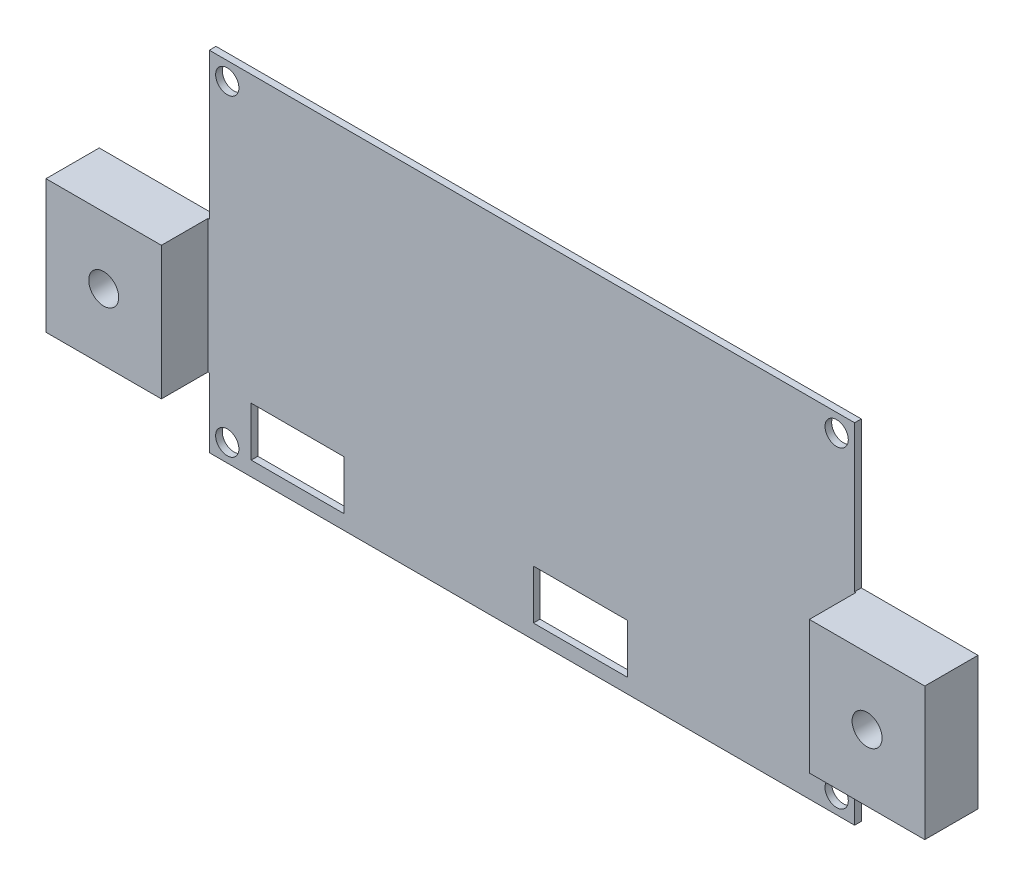
SolidWorks part; units mm, degrees
ref_plane "Front" through (0, 0, 0) normal (0, 0, 1) x (1, 0, 0)
ref_plane "Top" through (0, 0, 0) normal (0, 1, 0) x (1, 0, 0)
ref_plane "Right" through (0, 0, 0) normal (1, 0, 0) x (0, 0, -1)
sketch "Skizze1" plane through (0, 0, 0) normal (0, 0, 1) x (1, 0, 0)
  line L1 (0, 0) -> (97, 0)
  line L2 (0, 0) -> (0, 10.4)
  line L3 (0, 52.4) -> (97, 52.4)
  line L4 (97, 0) -> (97, 10.4)
  line L5 (6.2985, 2.1859) -> (20.2146, 2.1859)
  line L6 (6.2985, 2.1859) -> (6.2985, 9.5996)
  line L7 (6.2985, 9.5996) -> (20.2146, 9.5996)
  line L8 (20.2146, 2.1859) -> (20.2146, 9.5996)
  line L9 (48.5, 0) -> (48.5, -12.9781) construction
  line L11 (62.8756, 2.1859) -> (48.7166, 2.1859)
  line L12 (62.8756, 2.1859) -> (62.8756, 9.5996)
  line L13 (62.8756, 9.5996) -> (48.7166, 9.5996)
  line L14 (48.7166, 2.1859) -> (48.7166, 9.5996)
  line L15 (0, 30.4) -> (-17.5477, 30.4)
  line L16 (136.8695, 30.4) -> (-63.1305, 30.4) construction
  line L17 (-17.5477, 30.4) -> (-17.5477, 10.4)
  line L18 (136.8695, 10.4) -> (-63.1305, 10.4) construction
  line L19 (-17.5477, 10.4) -> (0, 10.4)
  line L20 (0, 30.4) -> (0, 52.4)
  line L21 (114.5477, 10.4) -> (97, 10.4)
  line L22 (114.5477, 30.4) -> (114.5477, 10.4)
  line L23 (97, 30.4) -> (114.5477, 30.4)
  line L24 (97, 30.4) -> (97, 52.4)
  circle A0 centre (94.3, 49.7) radius 1.75
  circle A1 centre (94.3, 2.7) radius 1.75
  circle A2 centre (2.7, 2.7) radius 1.75
  circle A3 centre (2.7, 49.7) radius 1.75
  point P40 (48.7166, 9.5996)
  dimension "D1" = 3.5
extrude "Aufsatz-Linear austragen1" add sketch "Skizze1" along normal blind 1
sketch "Skizze2" plane through (0, 0, 1) normal (0, 0, 1) x (1, 0, 0)
  line L0 (-17.5477, 30.4) -> (-17.5477, 10.4)
  line L1 (-17.5477, 10.4) -> (-0.2, 10.4)
  line L2 (-17.5477, 10.4) -> (0, 10.4) construction
  line L3 (-0.2, 10.4) -> (-0.2, 30.4)
  line L4 (0, 30.4) -> (-17.5477, 30.4) construction
  line L5 (-0.2, 30.4) -> (-17.5477, 30.4)
  line L6 (0, 52.4) -> (0, 0) construction
  line L7 (48.5, 0) -> (48.5, -21.6897)
  line L8 (0, 0) -> (97, 0) construction
  line L9 (97.2, 30.4) -> (114.5477, 30.4)
  line L10 (97.2, 10.4) -> (97.2, 30.4)
  line L11 (114.5477, 10.4) -> (97.2, 10.4)
  line L12 (114.5477, 30.4) -> (114.5477, 10.4)
  line M10 (97, 10.4) -> (114.5477, 10.4)
  line M11 (114.5477, 10.4) -> (114.5477, 30.4)
  line M12 (114.5477, 30.4) -> (97, 30.4)
  line M16 (0, 30.4) -> (-17.5477, 30.4)
  line M17 (-17.5477, 30.4) -> (-17.5477, 10.4)
  line M18 (-17.5477, 10.4) -> (0, 10.4)
  dimension "D1" = 0.2
extrude "Aufsatz-Linear austragen2" add sketch "Skizze2" along normal blind 7 contours L3 M18 M16 M17 | L10 M10 M11 M12
sketch "Skizze3" plane through (0, 0, 8) normal (0, 0, 1) x (1, 0, 0)
  line L0 (-17.5477, 20.4) -> (-0.2, 20.4) construction
  line L1 (-17.5477, 30.4) -> (-17.5477, 10.4) construction
  line L2 (-0.2, 10.4) -> (-0.2, 30.4) construction
  line L3 (48.5, 52.4) -> (48.5, 26.0168) construction
  line L4 (97, 52.4) -> (0, 52.4) construction
  circle A0 centre (-8.8739, 20.4) radius 2.25
  circle A1 centre (105.8739, 20.4) radius 2.25
  dimension "D1" = 4.5
extrude "Schnitt-Linear austragen1" cut sketch "Skizze3" against normal through all
